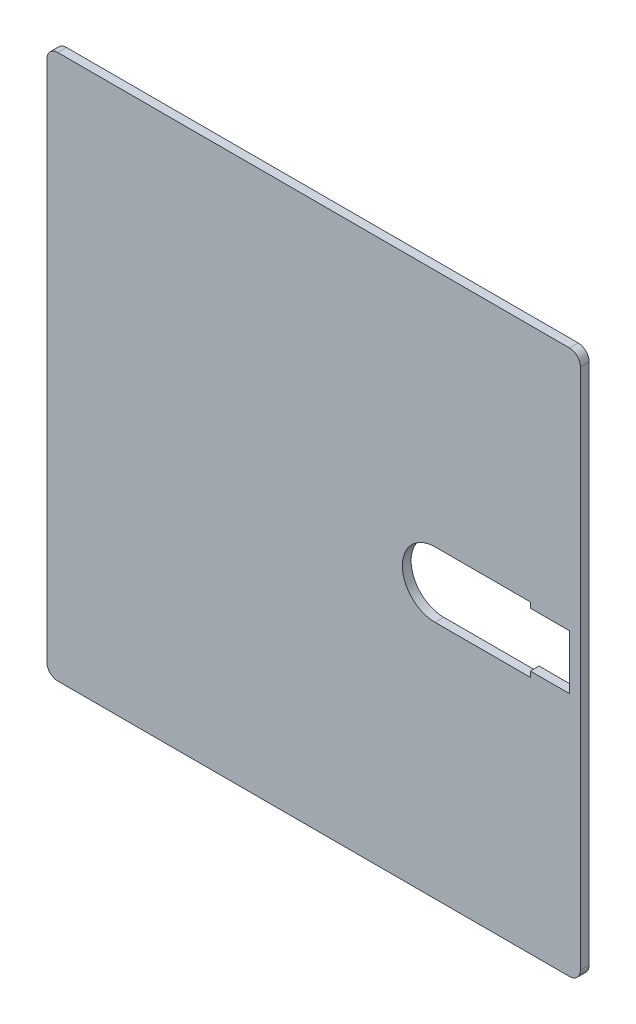
SolidWorks part; units mm, degrees
ref_plane "Front" through (0, 0, 0) normal (0, 0, 1) x (1, 0, 0)
ref_plane "Top" through (0, 0, 0) normal (0, 1, 0) x (1, 0, 0)
ref_plane "Right" through (0, 0, 0) normal (1, 0, 0) x (0, 0, -1)
sketch "草图1" plane through (0, 0, 0) normal (0, 0, 1) x (1, 0, 0)
  line L1 (0, 0) -> (98, 0)
  line L2 (0, 0) -> (0, 100)
  line L3 (0, 100) -> (98, 100)
  line L4 (98, 0) -> (98, 100)
  line L5 (96, 50) -> (88.8, 50)
  line L6 (96, 50) -> (96, 55)
  line L7 (96, 55) -> (88.8, 55)
  line L8 (88.8, 50) -> (88.8, 55)
  line L9 (96, 50) -> (88.8, 50)
  line L10 (96, 50) -> (96, 45)
  line L11 (96, 45) -> (88.8, 45)
  line L12 (88.8, 50) -> (88.8, 45)
  line L13 (88.8, 50) -> (71.3, 50)
  line L14 (88.8, 50) -> (88.8, 56)
  line L15 (88.8, 56) -> (71.3, 56)
  line L16 (71.3, 50) -> (71.3, 56)
  line L17 (88.8, 50) -> (71.3, 50)
  line L18 (88.8, 50) -> (88.8, 44)
  line L19 (88.8, 44) -> (71.3, 44)
  line L20 (71.3, 50) -> (71.3, 44)
  circle A0 centre (71.3, 50) radius 6
  point P11 (98, 50)
  dimension "D1" = 100
  dimension "D2" = 98
  dimension "D3" = 2
  dimension "D4" = 5
  dimension "D5" = 5
  dimension "D6" = 0
  dimension "D7" = 7.2
  dimension "D8" = 17.5
  dimension "D9" = 6
  dimension "D10" = 6
extrude "凸台-拉伸1" add sketch "草图1" along normal blind 1.6 contours L1 L4 L3 L2 A0 L15 L14 L7 L6 L10 L11 L18 L19
fillet "圆角1" radius 2 4 edges at (98, 0, 0.8) (0, 0, 0.8) (0, 100, 0.8) (98, 100, 0.8)
